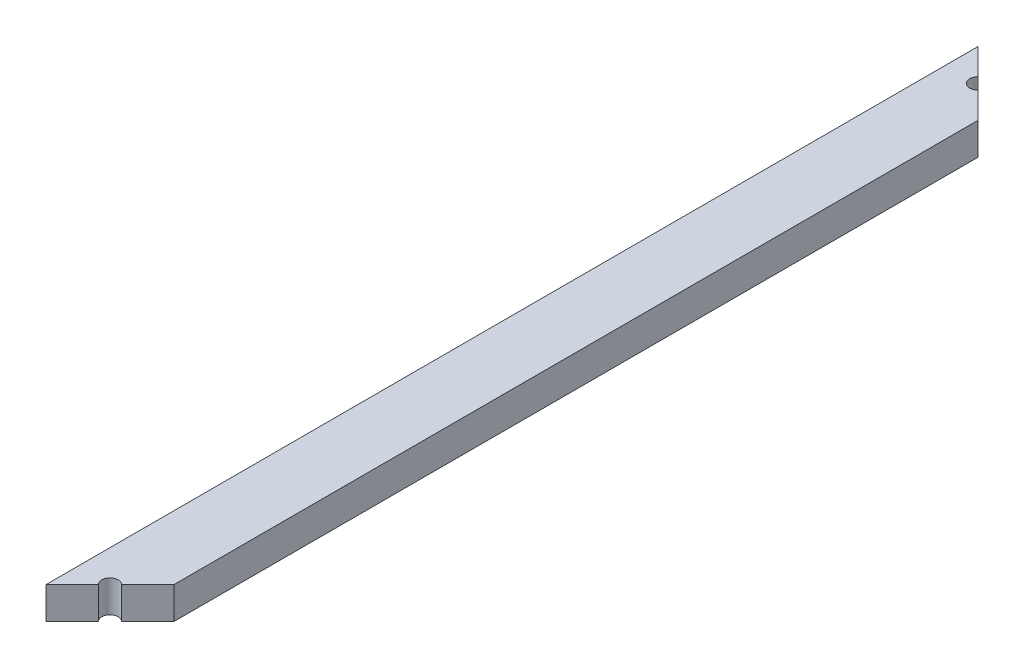
SolidWorks part; units mm, degrees
ref_plane "Front Plane" through (0, 0, 0) normal (0, 0, 1) x (1, 0, 0)
ref_plane "Top Plane" through (0, 0, 0) normal (0, 1, 0) x (1, 0, 0)
ref_plane "Right Plane" through (0, 0, 0) normal (1, 0, 0) x (0, 0, -1)
sketch "Sketch1" plane through (0, 0, 0) normal (0, 0, 1) x (1, 0, 0)
  line L1 (0, 0) -> (14, 0)
  line L2 (0, 0) -> (0, 7)
  line L3 (0, 7) -> (14, 7)
  line L4 (14, 0) -> (14, 7)
  dimension "D1" = 7
  dimension "D2" = 14
extrude "Boss-Extrude1" add sketch "Sketch1" along normal blind 204
sketch "Sketch2" plane through (0, 7, 0) normal (0, 1, 0) x (1, 0, 0)
  line L0 (0, 0) -> (14, -14)
  line L1 (14, -204) -> (14, 0) construction
  line L2 (14, -14) -> (14, 0)
  line L3 (14, 0) -> (0, 0)
  line L4 (0, -102) -> (14, -102) construction
  line L5 (0, -204) -> (0, 0) construction
  line L6 (14, -204) -> (0, -204)
  line L7 (14, -190) -> (14, -204)
  line L8 (0, -204) -> (14, -190)
  dimension "D1" = 45
extrude "Cut-Extrude1" cut sketch "Sketch2" against normal through all
sketch "Sketch3" plane through (0, 7, 0) normal (0, 1, 0) x (1, 0, 0)
  line L0 (0, 0) -> (14, -14) construction
  line L1 (0, -102) -> (14, -102) construction
  line L2 (0, -204) -> (0, 0) construction
  line L3 (14, -190) -> (14, -14) construction
  line L4 (14, -190) -> (0, -204) construction
  line L5 (8.2728, -195.7272) -> (5.7272, -198.2728)
  line L6 (5.7272, -5.7272) -> (8.2728, -8.2728)
  arc A0 (5.7272, -5.7272) -> (8.2728, -8.2728) centre (7, -7) ccw
  arc A1 (5.7272, -198.2728) -> (8.2728, -195.7272) centre (7, -197) cw
  dimension "D1" = 3.6
extrude "Cut-Extrude2" cut sketch "Sketch3" against normal through all
